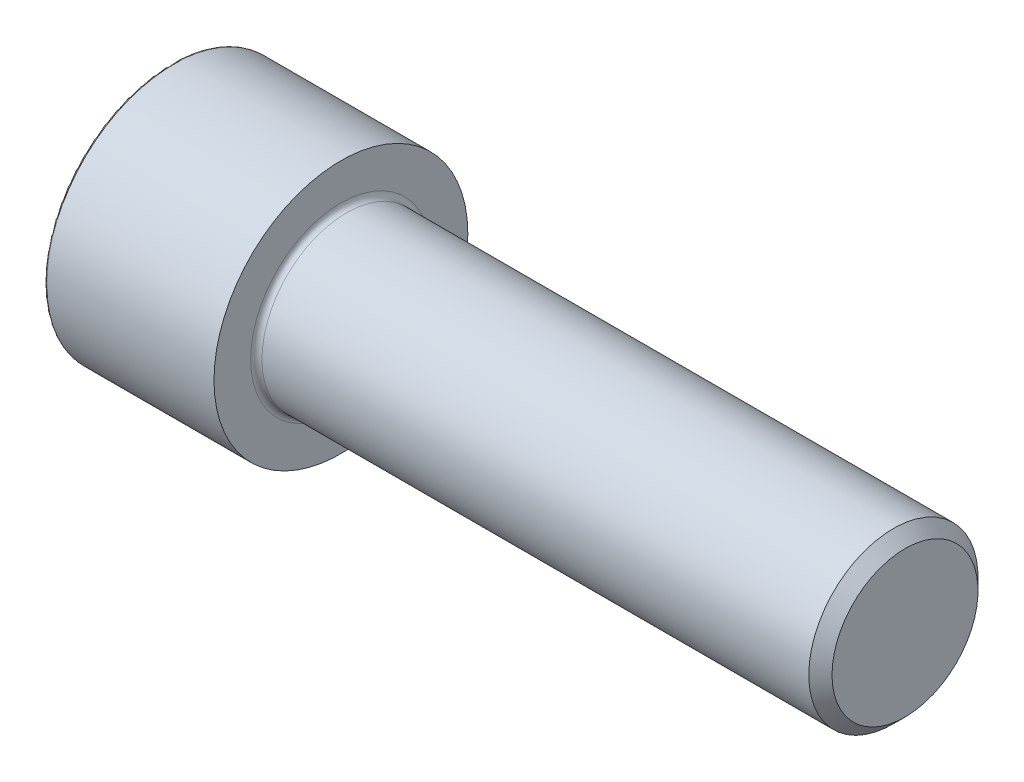
SolidWorks part; units mm, degrees
revolve "Base-Revolve" add sketch "BodySke"
sketch "BodySke" plane through (0, 0, 0) normal (0, 0, 1) x (1, 0, 0)
  line L0 (0, 0) -> (0, 18)
  line L1 (0, 18) -> (24, 18)
  line L2 (24, 18) -> (24, 12)
  line L3 (24, 12) -> (102.352, 12)
  line L4 (104, 10.352) -> (104, 0)
  line L5 (104, 0) -> (0, 0)
  line L6 (-31.75, 0) -> (127, 0) construction
  line L8 (104, 10.352) -> (102.352, 12)
  line L10 (104, -10.352) -> (102.352, -12) construction
  line L11 (27, 9.525) -> (27, 3.175) construction
  line L12 (44, 9.525) -> (44, 3.175) construction
  line L13 (44, 9.525) -> (44, 3.175) construction
  dimension "Body_ch_ang" = 45
  dimension "Thread_length" = 60
cosmetic thread "ThreadCosmetic"
fillet "Fillet1" radius 0.8 1 edges at (24, 0, 12)
fillet "Fillet2" radius 0.3 1 edges at (0, 0, 18)
ref_plane "Plane1" through (0, 0, 0) normal (0, 0, 1) x (1, 0, 0)
ref_plane "Plane2" through (0, 0, 0) normal (0, 1, 0) x (1, 0, 0)
ref_plane "Plane3" through (0, 0, 0) normal (1, 0, 0) x (0, 0, -1)
other "Configuration Table"
sketch "Sketch2" plane through (0, 0, 0) normal (0, 0, 1) x (1, 0, 0)
  line L0 (0, 9.6375) -> (12.573, 9.6375)
  line L1 (12.573, 9.6375) -> (18.1372, 0)
  line L2 (-31.75, 0) -> (127, 0) construction
  line L3 (18.1372, 0) -> (0, 0)
  line L4 (0, 0) -> (0, 9.6375)
  line L6 (0, 0) -> (47.625, 0) construction
  dimension "D2" = 60
revolve "Hex-PreBroach" cut sketch "Sketch2" angle 360 about L6
sketch "Sketch3" plane through (0, 0, 0) normal (-1, 0, 0) x (0, 0.5, 0.866)
  line L0 (5.5642, 9.6375) -> (-5.5642, 9.6375)
  line L1 (-5.5642, 9.6375) -> (-11.1284, 0)
  line L2 (5.5642, 9.6375) -> (11.1284, 0)
  line L3 (5.5642, -9.6375) -> (11.1284, 0)
  line L4 (5.5642, -9.6375) -> (-5.5642, -9.6375)
  line L5 (-5.5642, -9.6375) -> (-11.1284, 0)
extrude "Hex" cut sketch "Sketch3" against normal blind 12.573
sketch "ThdSchSke" plane through (0, 0, 0) normal (0, 0, 1) x (1, 0, 0)
  line L0 (44, -10.352) -> (42.8461, -12)
  line L1 (44, -10.352) -> (45.1539, -12)
  line L2 (45.1539, -12) -> (45.1539, -15)
  line L3 (-3.175, 0) -> (5.1513, 0) construction
  line L4 (0, 17.7) -> (0, -17.7) construction
  line L5 (45.1539, -15) -> (42.8461, -15)
  line L6 (42.8461, -15) -> (42.8461, -12)
revolve "ThreadSchematic" [suppressed] cut sketch "ThdSchSke" angle 360 about L3
pattern_linear "ThdSchPat" [suppressed]
equation "\"D2@Sketch3\" = \"Hex_size@Sketch3\" / 2"
equation "\"D1@Sketch3\" = \"Hex_size@Sketch3\" / 2"
equation "\"D1@Sketch2\" = \"Hex_size@Sketch3\" / 2"
equation "\"Thread_minor@ThreadCosmetic\"  =  \"Minor_dia@BodySke\""
equation "\"Depth@Sketch2\" =  \"Key_eng@Hex\""
equation "\"Thread_length@ThreadCosmetic\" = ((sgn( (\"Length@BodySke\" - \"Advance@BodySke\" * 3.0) - \"Thread_nom@BodySke\" )-1)*( (\"Length@BodySke\" - \"Advance@BodySke\" * 3.0) - \"Thread_nom@BodySke\" ))/-2+ \"Thread_nom@BodySke\""
equation "\"Thread_minor@ThdSchSke\" = \"Minor_dia@BodySke\""
equation "\"Diameter@ThdSchSke\" = \"Diameter@BodySke\""
equation "\"Overcut@ThdSchSke\" = \"Diameter@BodySke\" * 1.25"
equation "\"Start@ThdSchSke\" = \"Head_ht@BodySke\" + \"Length@BodySke\" - \"Thread_length@ThreadCosmetic\"  '---Non-countersunk---"
equation "\"Num_threads@ThdSchPat\" = int( \"Thread_length@ThreadCosmetic\" / \"Advance@BodySke\" + 0.999 )  + 1"
equation "\"Advance@ThdSchPat\" = \"Thread_length@ThreadCosmetic\" /  (\"Num_threads@ThdSchPat\" - 1) 'relax it"
equation "\"Num_threads@ThdSchPat\" = \"Num_threads@ThdSchPat\" - sgn( \"Num_threads@ThdSchPat\" - 1) '---chamfered tips only---"
